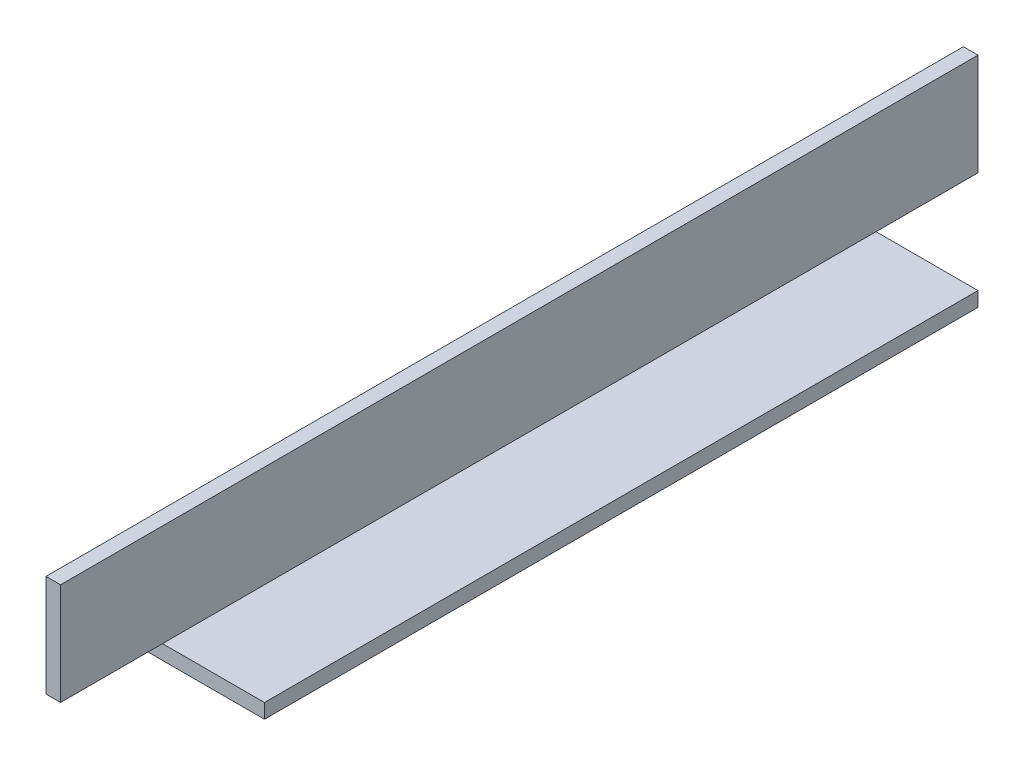
SolidWorks part; units mm, degrees
ref_plane "Front Plane" through (0, 0, 0) normal (0, 0, 1) x (1, 0, 0)
ref_plane "Top Plane" through (0, 0, 0) normal (0, 1, 0) x (1, 0, 0)
ref_plane "Right Plane" through (0, 0, 0) normal (1, 0, 0) x (0, 0, -1)
sketch "Sketch1" plane through (0, 0, 0) normal (0, 0, 1) x (1, 0, 0)
  line L0 (0, 25.4) -> (0, 0) construction
  line L1 (0, 0) -> (25.4, 0) construction
  line L2 (25.4, 0) -> (25.4, 3.175) construction
  line L3 (25.4, 3.175) -> (3.175, 3.175) construction
  line L4 (3.175, 3.175) -> (3.175, 25.4) construction
  line L6 (3.175, 25.4) -> (0, 25.4) construction
  arc A0 (3.175, 3.5814) -> (3.5814, 3.175) centre (3.5814, 3.5814) ccw construction
  point P4 (0, 0)
  dimension "Inside Corner Radius" = 0.4064
  dimension "Outside Height" = 25.4
  dimension "Inside Height" = 22.225
  dimension "Outside Width" = 25.4
  dimension "Inside Width" = 22.225
  dimension "Wall Thickness" = 3.175
  dimension "Shape" = 90
sketch "Sketch2" plane through (0, 0, 0) normal (1, 0, 0) x (0, 0, -1)
  line L0 (1219.2, 0) -> (-1219.2, 0) construction
  line L1 (-1219.2, 25.4) -> (-1219.2, 0) construction
  line L2 (1219.2, 25.4) -> (1219.2, 0) construction
  point P0 (-1189.99, 0)
  point P4 (0, 0)
  point P6 (1189.99, 0)
  dimension "D1" = 29.21
  dimension "D2" = 29.21
  dimension "D3" = 25.4
  dimension "Length" = 2438.4
sketch "Sketch3" plane through (0, 0, 0) normal (0, 0, 1) x (1, 0, 0)
  line L0 (3.175, 25.4) -> (0, 25.4)
  line L1 (0, 25.4) -> (0, 0)
  line L2 (0, 0) -> (25.4, 0)
  line L3 (25.4, 0) -> (25.4, 3.175)
  line L4 (25.4, 3.175) -> (3.175, 3.175)
  line L5 (3.175, 3.175) -> (3.175, 25.4)
extrude "Boss-Extrude1" add sketch "Sketch3" along normal mid plane 2438.4
fillet "Fillet1" radius 0.4064 1 edges at (3.175, 3.175, 0)
sketch "Sketch4" plane through (0, 0, 0) normal (-1, 0, 0) x (0, 0, 1)
  line L0 (1219.2, 25.4) -> (1219.2, 0) construction
  line L1 (-1219.2, 25.4) -> (1019.2, 25.4)
  line L2 (-1219.2, 25.4) -> (-1219.2, -77.8785)
  line L3 (-1219.2, -77.8785) -> (1019.2, -77.8785)
  line L4 (1019.2, 25.4) -> (1019.2, -77.8785)
  dimension "D1" = 200
extrude "Cut-Extrude1" cut sketch "Sketch4" against normal blind 60
sketch "Sketch5" plane through (0, 0, 0) normal (0, -1, 0) x (1, 0, 0)
  line L0 (0, 1219.2) -> (0, 1019.2) construction
  line L1 (25.4, 1019.2) -> (0, 1019.2)
  line L2 (25.4, 1019.2) -> (25.4, 1041.43)
  line L3 (25.4, 1041.43) -> (0, 1041.43)
  line L4 (0, 1019.2) -> (0, 1041.43)
  dimension "D1" = 22.23
extrude "Cut-Extrude2" cut sketch "Sketch5" against normal up to surface (3.175 mm away) up to face at (14.4907, 3.175, 1119.2)
sketch "Sketch6" plane through (0, 0, 0) normal (0, -1, 0) x (1, 0, 0)
  line L0 (0, 1219.2) -> (0, 1041.43) construction
  line L1 (25.4, 1219.2) -> (0, 1219.2)
  line L2 (25.4, 1219.2) -> (25.4, 1196.97)
  line L3 (25.4, 1196.97) -> (0, 1196.97)
  line L4 (0, 1219.2) -> (0, 1196.97)
  dimension "D1" = 22.23
extrude "Cut-Extrude3" cut sketch "Sketch6" against normal up to surface (3.175 mm away) up to face at (14.4907, 3.175, 1130.315)
sketch "Sketch7" plane through (0, 0, 1019.2) normal (0, 0, -1) x (-1, 0, 0)
  line L0 (-3.175, 3.5814) -> (-3.175, 25.4) construction
  line L1 (-3.175, 4.2) -> (-4.4439, 4.2)
  line L2 (-3.175, 4.2) -> (-3.175, 3.175)
  line L3 (-3.175, 3.175) -> (-4.4439, 3.175)
  line L4 (-4.4439, 4.2) -> (-4.4439, 3.175)
  line L5 (-3.5814, 3.175) -> (-25.4, 3.175) construction
extrude "Cut-Extrude4" cut sketch "Sketch7" against normal blind 220
equation "\"D1@Boss-Extrude1\"=\"Length@Sketch2\""
equation "\"D1@Sketch2\" = \"Outside Width@Sketch1\" * 1.15"
equation "\"D2@Sketch2\"=\"D1@Sketch2\""
equation "\"D1@Fillet1\"=\"Inside Corner Radius@Sketch1\""
equation "\"D3@Sketch2\"=\"Outside Height@Sketch1\""
